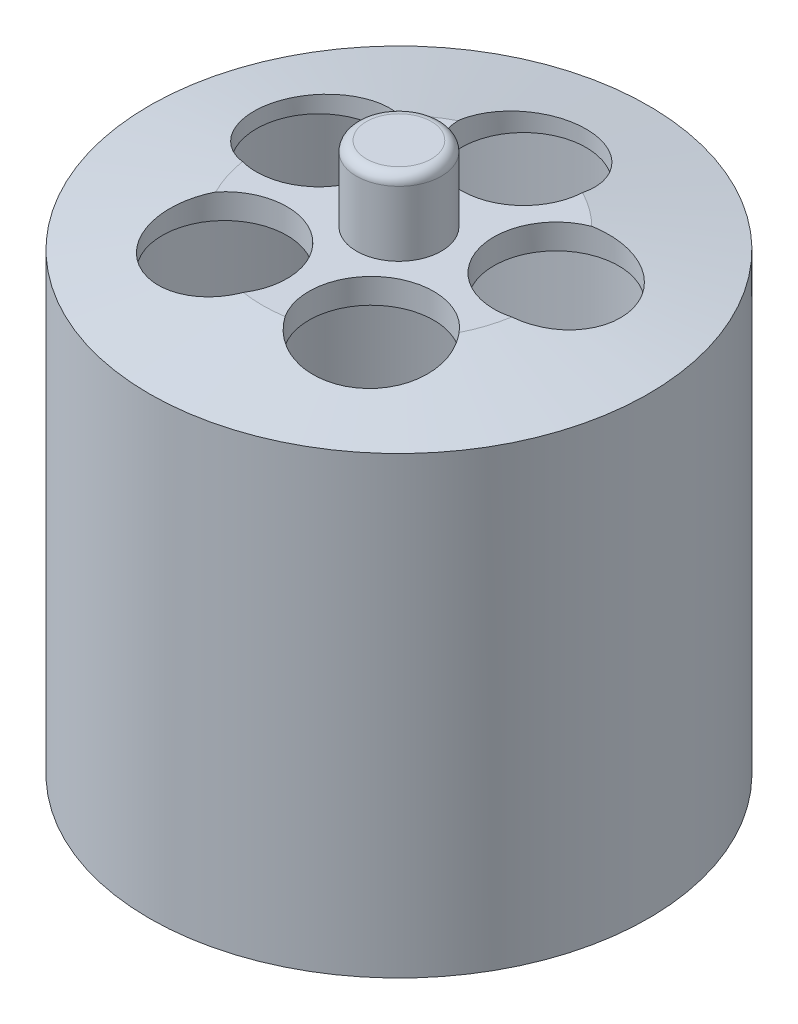
SolidWorks part; units mm, degrees
ref_plane "Front Plane" through (0, 0, 0) normal (0, 0, 1) x (1, 0, 0)
ref_plane "Top Plane" through (0, 0, 0) normal (0, 1, 0) x (1, 0, 0)
ref_plane "Right Plane" through (0, 0, 0) normal (1, 0, 0) x (0, 0, -1)
sketch "Sketch1" plane through (0, 0, 0) normal (0, 1, 0) x (1, 0, 0)
  circle A0 centre (0, 0) radius 50.8
  circle A1 centre (0, 0) radius 63.5
  dimension "D1" = 12.7
  dimension "D2" = 127
extrude "Boss-Extrude1" add sketch "Sketch1" along normal blind 114.3
sketch "Sketch2" plane through (0, 114.3, 0) normal (0, 1, 0) x (1, 0, 0)
  circle A0 centre (0, 0) radius 63.5
extrude "Boss-Extrude2" add sketch "Sketch2" along normal blind 6.35
chamfer "Chamfer1" distance 5.08 angle 80 1 edges at (0, 120.65, 63.5)
sketch "Sketch3" plane through (0, 120.65, 0) normal (0, 1, 0) x (1, 0, 0)
  circle A0 centre (0, 31.75) radius 15.875
  circle A1 centre (30.196, 9.8113) radius 15.875
  circle A2 centre (18.6622, -25.6863) radius 15.875
  circle A3 centre (-18.6622, -25.6863) radius 15.875
  circle A4 centre (-30.196, 9.8113) radius 15.875
  point P12 (0, 0)
  dimension "D1" = 31.75
  dimension "D3" = 31.75
  dimension "D2" = 5
extrude "Cut-Extrude1" cut sketch "Sketch3" against normal through all
sketch "Sketch4" plane through (0, 120.65, 0) normal (0, 1, 0) x (1, 0, 0)
  circle A0 centre (0, 0) radius 10.795
  dimension "D1" = 21.59
extrude "Boss-Extrude3" add sketch "Sketch4" along normal blind 19.05
fillet "Fillet1" radius 2.54 1 edges at (0, 139.7, 10.795)
